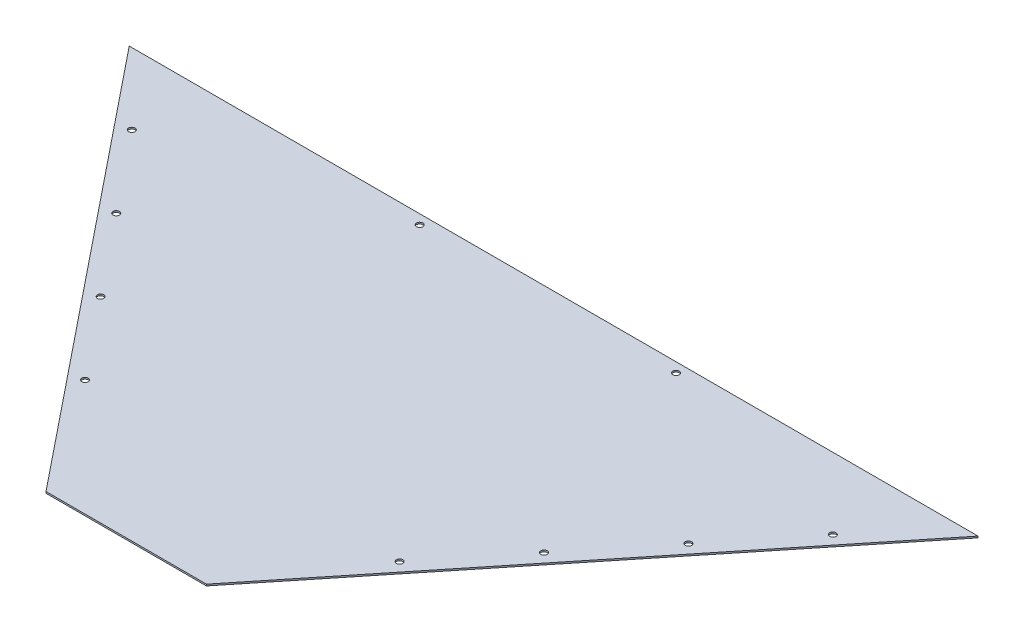
SolidWorks part; units mm, degrees
ref_plane "Front Plane" through (0, 0, 0) normal (0, 0, 1) x (1, 0, 0)
ref_plane "Top Plane" through (0, 0, 0) normal (0, 1, 0) x (1, 0, 0)
ref_plane "Right Plane" through (0, 0, 0) normal (1, 0, 0) x (0, 0, -1)
sketch "Sketch1" plane through (0, 0, 0) normal (0, 1, 0) x (1, 0, 0)
  line L0 (0, 0) -> (317.5, 0)
  line L1 (317.5, 0) -> (998.5375, 845.7294)
  line L3 (998.5375, 845.7294) -> (-681.0375, 845.7294)
  line L5 (-681.0375, 845.7294) -> (0, 0)
  line L6 (158.75, 845.7294) -> (158.75, 0) construction
  dimension "D1" = 317.5
  dimension "D2" = 1085.85
  dimension "D4" = 1679.575
extrude "Boss-Extrude1" add sketch "Sketch1" along normal blind 3.175
sketch "Sketch2" plane through (0, 3.175, 0) normal (0, 1, 0) x (-1, 0, 0)
  line L0 (-158.75, -845.7294) -> (-158.75, 0) construction
  line L1 (-998.5375, -845.7294) -> (681.0375, -845.7294) construction
  line L2 (0, 0) -> (-317.5, 0) construction
  circle A0 centre (87.1855, -826.6794) radius 6.35
  circle A1 centre (-420.1795, -826.6794) radius 6.35
  dimension "D1" = 593.852
  dimension "D2" = 12.7
  dimension "D4" = 19.05
  dimension "D5" = 578.358
  dimension "D3" = 19.05
extrude "Cut-Extrude1" cut sketch "Sketch2" against normal up to next
sketch "Sketch3" plane through (0, 3.175, 0) normal (0, 1, 0) x (1, 0, 0)
  line L5 (998.5375, 845.7294) -> (990.6, 845.7294)
  line L6 (998.5375, 845.7294) -> (-681.0375, 845.7294) construction
  line L7 (990.6, 845.7294) -> (990.6, 835.8724)
  line L8 (317.5, 0) -> (998.5375, 845.7294) construction
  line L9 (990.6, 835.8724) -> (998.5375, 845.7294)
sketch "Sketch4" plane through (0, 3.175, 0) normal (0, 1, 0) x (1, 0, 0)
  line L0 (317.5, 0) -> (998.5375, 845.7294) construction
  line L1 (158.75, 845.7294) -> (158.75, 0) construction
  line L2 (998.5375, 845.7294) -> (-681.0375, 845.7294) construction
  line L3 (0, 0) -> (317.5, 0) construction
  circle A0 centre (852.3083, 704.6362) radius 6.35
  circle A1 centre (469.9715, 229.8408) radius 6.35
  circle A2 centre (724.8627, 546.3711) radius 6.35
  circle A3 centre (597.4171, 388.1059) radius 6.35
  circle A4 centre (-534.8083, 704.6362) radius 6.35
  circle A5 centre (-407.3627, 546.3711) radius 6.35
  circle A6 centre (-279.9171, 388.1059) radius 6.35
  circle A7 centre (-152.4715, 229.8408) radius 6.35
  dimension "D1" = 25.4
  dimension "D2" = 203.2
  dimension "D3" = 25.4
  dimension "D4" = 609.6
  dimension "D5" = 25.4
  dimension "D6" = 25.4
  dimension "D7" = 203.2
  dimension "D8" = 203.2
extrude "Cut-Extrude2" cut sketch "Sketch4" against normal through all
